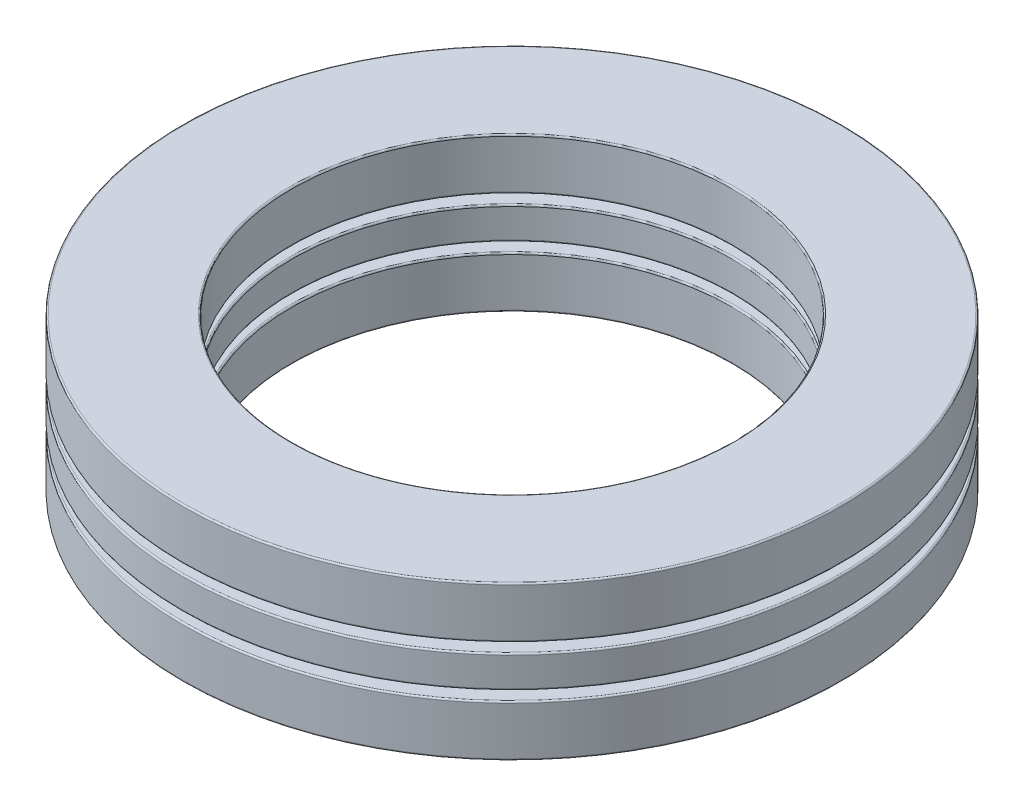
SolidWorks part; units mm, degrees
ref_plane "Front Plane" through (0, 0, 0) normal (0, 0, 1) x (1, 0, 0)
ref_plane "Top Plane" through (0, 0, 0) normal (0, 1, 0) x (1, 0, 0)
ref_plane "Right Plane" through (0, 0, 0) normal (1, 0, 0) x (0, 0, -1)
sketch "Sketch1" plane through (0, 0, 0) normal (1, 0, 0) x (0, 0, -1)
  line L0 (-23.8125, 0) -> (23.8125, 0) construction
  line L1 (0, -5.5499) -> (0, 5.5499) construction
  line L2 (-23.8125, 1.1562) -> (-15.9131, 1.1562)
  line L3 (-23.8125, 1.1562) -> (-23.8125, -1.1562)
  line L4 (-23.8125, -1.1562) -> (-15.9131, -1.1562)
  line L5 (-15.9131, 1.1562) -> (-15.9131, -1.1562)
  line L6 (-19.8628, 1.85) -> (-19.8628, -1.85) construction
  circle A0 centre (-19.8628, 0) radius 1.85 construction
  point P13 (-19.8628, 1.1562)
  dimension "OD" = 47.625
  dimension "Shaft Dia" = 31.8262
  dimension "Th" = 11.0998
  dimension "D1" = 3.6999
  dimension "D2" = 2.3125
revolve "Revolve1" add sketch "Sketch1" angle 360 about L1
sketch "Sketch3" plane through (0, 0, 0) normal (1, 0, 0) x (0, 0, -1)
  line L0 (-19.8628, 1.85) -> (-19.8628, -1.85)
  arc A0 (-19.8628, 1.85) -> (-19.8628, -1.85) centre (-19.8628, 0) ccw
  circle A1 centre (-19.8628, 0) radius 1.85 construction
revolve "Cut-Revolve1" cut sketch "Sketch3" angle 360 about L0
sketch "Sketch2" plane through (0, 0, 0) normal (1, 0, 0) x (0, 0, -1)
  line L0 (-19.8628, 1.85) -> (-19.8628, -1.85)
  arc A0 (-19.8628, 1.85) -> (-19.8628, -1.85) centre (-19.8628, 0) ccw
  circle A2 centre (-19.8628, 0) radius 1.85 construction
revolve "Revolve2" add sketch "Sketch2" angle 360 about L0
ref_axis "Axis1" through (0, 5.5499, 0) along (0, -1, 0)
pattern_circular "CirPattern1" count 9 every 40 about axis through (0, 5.5499, 0) along (0, -1, 0) of bodies 187
pattern_circular "CirPattern2" count 9 every 40 about axis through (0, 0, 0) along (0, 1, 0) of "Cut-Revolve1"
sketch "Sketch4" plane through (0, 0, 0) normal (1, 0, 0) x (0, 0, -1)
  line L0 (-23.8125, 1.1562) -> (-23.8125, -1.1562) construction
  line L1 (-23.8125, 1.85) -> (-15.9131, 1.85)
  line L2 (-23.8125, 1.85) -> (-23.8125, 5.5499)
  line L3 (-23.8125, 5.5499) -> (-15.9131, 5.5499)
  line L4 (-15.9131, 1.85) -> (-15.9131, 5.5499)
  line L5 (-23.8125, -5.5499) -> (-15.9131, -5.5499)
  line L6 (-23.8125, -5.5499) -> (-23.8125, -1.85)
  line L7 (-23.8125, -1.85) -> (-15.9131, -1.85)
  line L8 (-15.9131, -5.5499) -> (-15.9131, -1.85)
  line L9 (-19.8628, 1.85) -> (-19.8628, -1.85) construction
  line L10 (-15.9131, 1.1562) -> (-15.9131, -1.1562) construction
  line L11 (0, 0) -> (-23.8125, 0) construction
  line L12 (-23.8125, 0) -> (23.8125, 0) construction
  dimension "Ht" = 11.0998
revolve "Revolve3" add sketch "Sketch4" angle 360 about L1
fillet "Fillet1" radius 0.111 4 edges at (0, 1.85, -15.9131) (0, 5.5499, -15.9131) (0, 1.85, -23.8125) (0, 5.5499, -23.8125)
fillet "Fillet2" radius 0.111 4 edges at (0, -1.1562, -15.9131) (0, 1.1562, -15.9131) (0, -1.1562, -23.8125) (0, 1.1562, -23.8125)
fillet "Fillet3" radius 0.111 4 edges at (0, -5.5499, -15.9131) (0, -1.85, -15.9131) (0, -5.5499, -23.8125) (0, -1.85, -23.8125)
equation "\"D1@Sketch1\" = \"Th@Sketch1\"/3"
equation "\"D2@Sketch1\" = \"D1@Sketch1\"*.625"
equation "\"Balls@CirPattern1\" = \"OD@Sketch1\"*5"
equation "\"Angle@CirPattern1\" = 360/\"Balls@CirPattern1\""
equation "\"D1@CirPattern2\" = \"Balls@CirPattern1\""
equation "\"D2@CirPattern2\" = \"Angle@CirPattern1\""
equation "\"D1@Fillet1\" = \"Th@Sketch1\"*.01"
equation "\"D1@Fillet2\" = \"D1@Fillet1\""
equation "\"D1@Fillet3\" = \"D1@Fillet1\""
